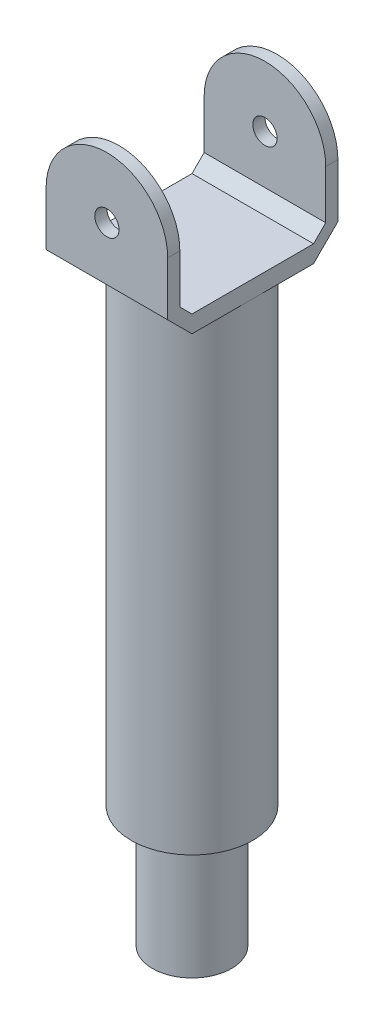
SolidWorks part; units mm, degrees
ref_plane "Front Plane" through (0, 0, 0) normal (0, 0, 1) x (1, 0, 0)
ref_plane "Top Plane" through (0, 0, 0) normal (0, 1, 0) x (1, 0, 0)
ref_plane "Right Plane" through (0, 0, 0) normal (1, 0, 0) x (0, 0, -1)
sketch "Sketch1" plane through (0, 0, 0) normal (0, 1, 0) x (1, 0, 0)
  circle A0 centre (0, 0) radius 32.5
  dimension "D1" = 65
extrude "Boss-Extrude1" add sketch "Sketch1" along normal blind 100
sketch "Sketch2" plane through (0, 100, 0) normal (0, 1, 0) x (1, 0, 0)
  circle A0 centre (0, 0) radius 50
  dimension "D1" = 100
extrude "Boss-Extrude2" add sketch "Sketch2" along normal blind 400
sketch "Sketch6" plane through (0, 0, 0) normal (1, 0, 0) x (0, 0, -1)
  line L0 (-50, 500) -> (-60, 510)
  line L1 (-60, 510) -> (-60, 600)
  line L2 (-60, 600) -> (-70, 600)
  line L3 (-70, 600) -> (-70, 505.8579)
  line L4 (-70, 505.8579) -> (-50, 485.8579)
  line L5 (-50, 500) -> (-50, 100) construction
  line L6 (-50, 485.8579) -> (50, 485.8579)
  line L7 (50, 100) -> (50, 500) construction
  line L8 (50, 485.8579) -> (70, 505.8579)
  line L9 (70, 505.8579) -> (70, 600)
  line L10 (70, 600) -> (60, 600)
  line L11 (60, 600) -> (60, 510)
  line L12 (60, 510) -> (50, 500)
  line L13 (50, 500) -> (-50, 500)
  dimension "D1" = 135
  dimension "D2" = 90
  dimension "D3" = 10
  dimension "D4" = 10
  dimension "D5" = 10
extrude "Boss-Extrude3" add sketch "Sketch6" along normal mid plane 100
sketch "Sketch7" plane through (0, 0, 70) normal (0, 0, 1) x (1, 0, 0)
  line L0 (-50, 600) -> (-50, 505.8579) construction
  line L1 (50, 600) -> (-50, 600) construction
  line L2 (50, 600) -> (50, 505.8579) construction
  line L3 (-50, 550) -> (-50, 605)
  line L4 (-50, 605) -> (50, 605)
  line L5 (50, 605) -> (50, 550)
  circle A0 centre (0, 550) radius 10
  arc A1 (50, 550) -> (-50, 550) centre (0, 550) ccw
  dimension "D1" = 5
  dimension "D2" = 20
extrude "Cut-Extrude2" cut sketch "Sketch7" against normal through all both and the other way through all
